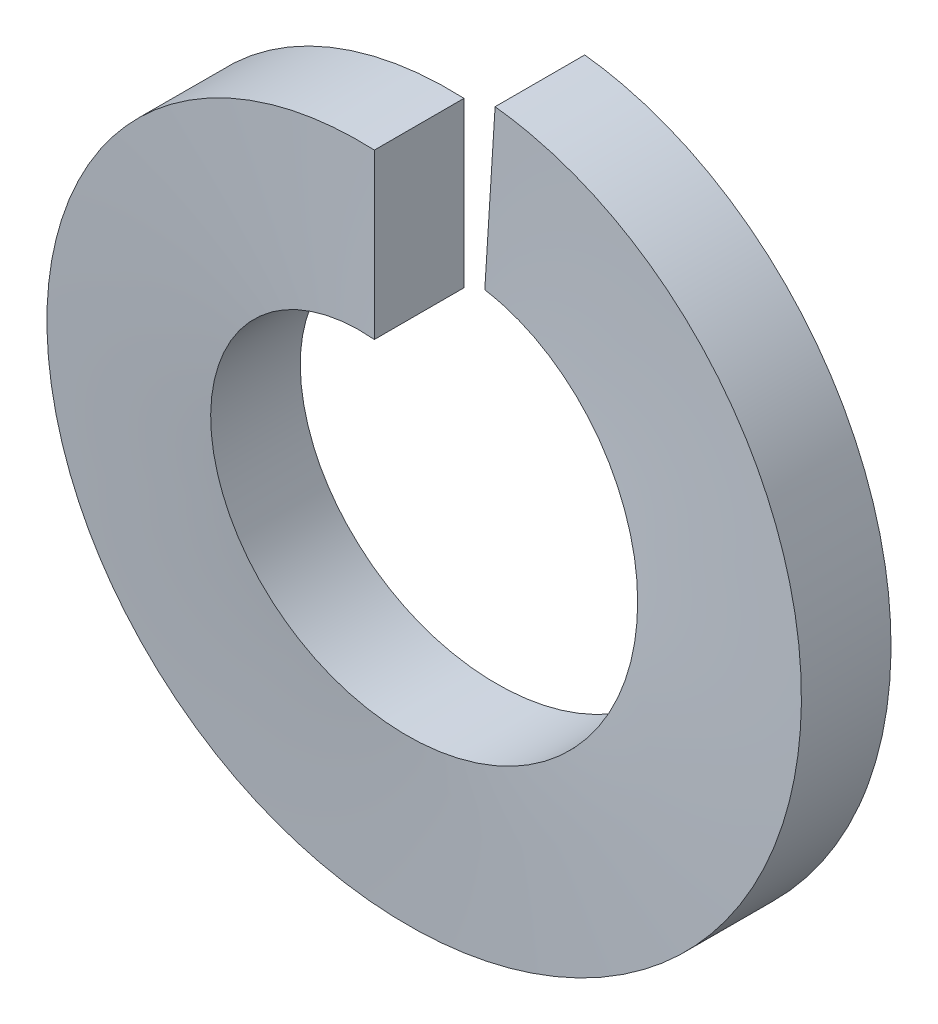
SolidWorks part; units mm, degrees
ref_plane "Front Plane" through (0, 0, 0) normal (0, 0, 1) x (1, 0, 0)
ref_plane "Top Plane" through (0, 0, 0) normal (0, 1, 0) x (1, 0, 0)
ref_plane "Right Plane" through (0, 0, 0) normal (1, 0, 0) x (0, 0, -1)
sketch "Sketch1" plane through (0, 0, 0) normal (0, 0, 1) x (1, 0, 0)
  line L0 (0, 6.1849) -> (0, 3.302) construction
  circle A0 centre (0, 0) radius 6.1849
  circle A1 centre (0, 0) radius 3.302 construction
  dimension "ID" = 6.604
  dimension "OD" = 12.3698
curve "Helix/Spiral1" pitch 1.7498 height 1.7323 turns 0.99 parameters "HT"=1.7323
sketch "Sketch2" plane through (0, 0, 0) normal (1, 0, 0) x (0, 0, -1)
  line L1 (0, 6.1849) -> (-1.5748, 6.1849)
  line L2 (0, 6.1849) -> (0, 3.302)
  line L3 (0, 3.302) -> (-1.5748, 3.302)
  line L4 (-1.5748, 6.1849) -> (-1.5748, 3.302)
  dimension "THK" = 1.5748
sweep "Sweep1" add profiles "Sketch2" path "Helix/Spiral1"
sketch "Sketch3" plane through (0, 0, 0) normal (0, 0, 1) x (1, 0, 0)
  circle A0 centre (0, 0) radius 3.302 construction
  spline S0 degree 2 poles (0, 3.302) (-1.0729, 3.302) (-1.941, 2.6713) (-2.809, 2.0407) (-3.1406, 1.0202) (-3.4721, -0.0002) (-3.1406, -1.0206) (-2.809, -2.0411) (-1.941, -2.6717) (-1.073, -3.3024) (0, -3.3024) (1.0729, -3.3024) (1.941, -2.6717) (2.809, -2.0411) (3.1406, -1.0206) (3.4721, -0.0002) (3.1406, 1.0202) (2.809, 2.0407) (1.941, 2.6713) (1.1648, 3.2352) (0.2074, 3.2955) (0.2074, 3.2955) (0.2074, 3.2955) knots 0 0 0 0.1 0.1 0.2 0.2 0.3 0.3 0.4 0.4 0.5 0.5 0.6 0.6 0.7 0.7 0.8 0.8 0.9 0.9 0.989879 0.989879 0.98988 0.98988 0.98988 weights 1 0.951057 1 0.951057 1 0.951057 1 0.951057 1 0.951057 1 0.951057 1 0.951057 1 0.951057 1 0.951057 1 0.95601 0.991096 0.991096 0.991096 construction
equation "\"HT@Helix/Spiral1\" = \"THK@Sketch2\"*1.1"
